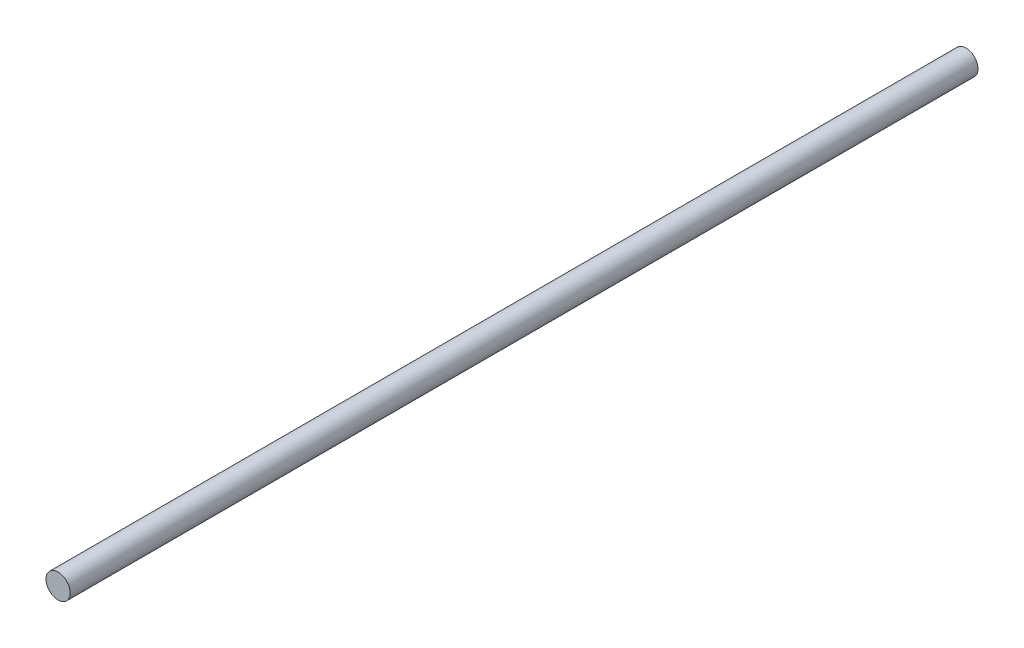
SolidWorks part; units mm, degrees
ref_plane "Front Plane" through (0, 0, 0) normal (0, 0, 1) x (1, 0, 0)
ref_plane "Top Plane" through (0, 0, 0) normal (0, 1, 0) x (1, 0, 0)
ref_plane "Right Plane" through (0, 0, 0) normal (1, 0, 0) x (0, 0, -1)
sketch "Sketch1" plane through (0, 0, 0) normal (0, 0, 1) x (1, 0, 0)
  circle A0 centre (0, 0) radius 3.175
  dimension "D1" = 6.35
extrude "Boss-Extrude1" add sketch "Sketch1" along normal blind 238.125
